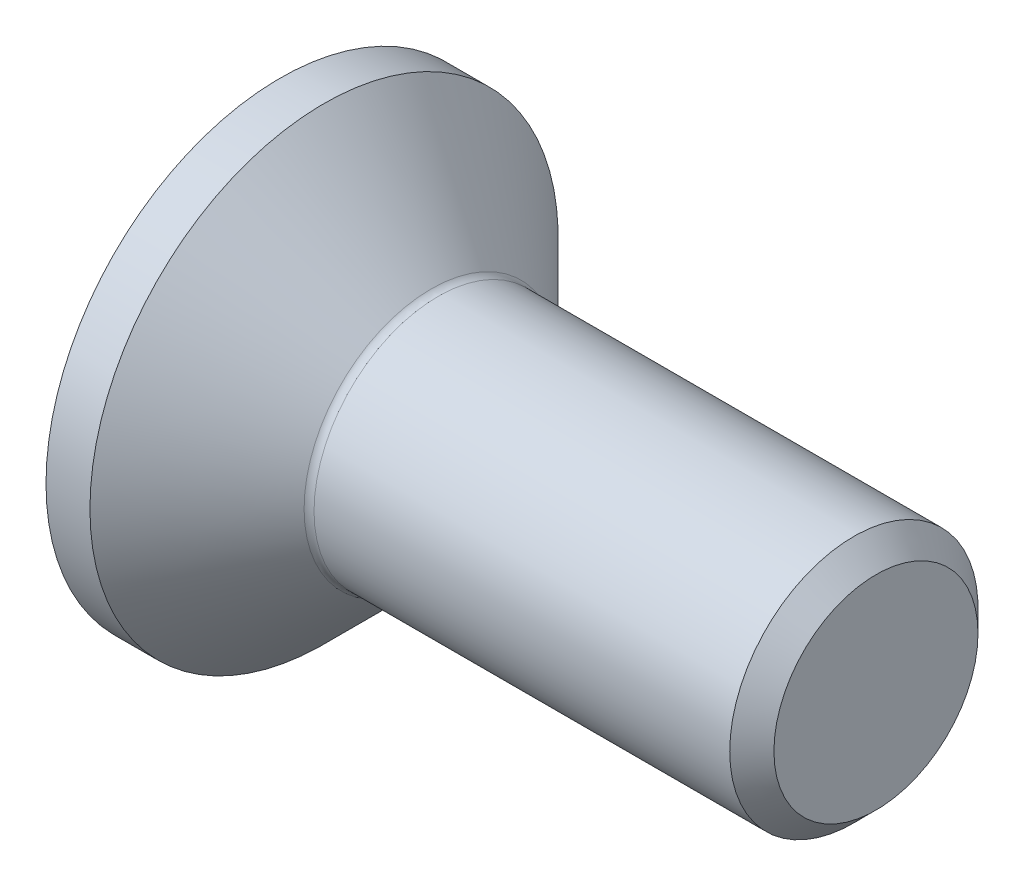
SolidWorks part; units mm, degrees
ref_plane "Plane1" through (0, 0, 0) normal (0, 0, 1) x (1, 0, 0)
ref_plane "Plane2" through (0, 0, 0) normal (0, 1, 0) x (1, 0, 0)
ref_plane "Plane3" through (0, 0, 0) normal (1, 0, 0) x (0, 0, -1)
sketch "BodySke" plane through (0, 0, 0) normal (0, 0, 1) x (1, 0, 0)
  line L0 (0, 0) -> (0, 4.715)
  line L1 (0.885, 4.715) -> (3.1, 2.5)
  line L2 (0, 4.715) -> (0.885, 4.715)
  line L3 (3.1, 2.5) -> (11.555, 2.5)
  line L4 (12, 2.055) -> (12, 0)
  line L5 (12, 0) -> (0, 0)
  line L6 (0, 0) -> (127, 0) construction
  line L7 (0.885, -4.715) -> (3.1, -2.5) construction
  line L8 (12, 2.055) -> (11.555, 2.5)
  line L9 (0, -4.715) -> (0.885, -4.715) construction
  line L10 (12, -2.055) -> (11.555, -2.5) construction
  line L11 (3.9, 8.85) -> (3.9, -13.375) construction
  line L12 (0, 19.05) -> (0, -3.175) construction
  dimension "D1" = 0.885
  dimension "Diameter" = 5
  dimension "Head_ht" = 3.1
  dimension "Length" = 12
  dimension "Body_ch_ang" = 45
  dimension "Head_dia" = 9.43
  dimension "Minor_dia" = 4.11
  dimension "Head_ang" = 90
  dimension "Advance" = 0.8
  dimension "Thread_nom" = 12
revolve "BaseBody" add sketch "BodySke"
cosmetic thread "ThreadCosmetic" [suppressed]
fillet "Fillet1" radius 0.2 1 edges at (3.1, 0, 2.5)
sketch "Sketch2" plane through (0, 0, 0) normal (0, 0, 1) x (1, 0, 0)
  line L0 (0, 1.5) -> (1.9, 1.5)
  line L1 (1.9, 1.5) -> (2.766, 0)
  line L2 (0, 0) -> (127, 0) construction
  line L3 (2.766, 0) -> (0, 0)
  line L4 (0, 0) -> (0, 1.5)
  line L5 (0, -1.5) -> (1.9, -1.5) construction
  line L6 (0, 0) -> (47.625, 0) construction
  line L8 (0, 4.715) -> (0, -4.715) construction
  dimension "D2" = 60
  dimension "PreBroach_depth" = 1.9
  dimension "PreBroach_dia" = 3
revolve "PreBroach" cut sketch "Sketch2" angle 360 about L6
sketch "Sketch3" plane through (0, 0, 0) normal (-1, 0, 0) x (0, 0, 1)
  line L0 (-1.5, -0.866) -> (-1.5, 0.866)
  line L1 (-1.5, 0.866) -> (0, 1.7321)
  line L2 (0, 1.7321) -> (1.5, 0.866)
  line L3 (1.5, 0.866) -> (1.5, -0.866)
  line L4 (1.5, -0.866) -> (0, -1.7321)
  line L5 (0, -1.7321) -> (-1.5, -0.866)
  dimension "D1" = 1.5
  dimension "D2" = 1.5
  dimension "D3" = 3
  dimension "Hex_size" = 3
extrude "Hex" cut sketch "Sketch3" against normal blind 1.9
sketch "ThdSchSke" [suppressed] plane through (0, 0, 0) normal (0, 0, 1) x (1, 0, 0)
  line L0 (5.5, -2.055) -> (5.1884, -2.5)
  line L1 (5.5, -2.055) -> (5.8116, -2.5)
  line L2 (5.8116, -2.5) -> (5.8116, -3.125)
  line L3 (-3.175, 0) -> (5.1513, 0) construction
  line L4 (0, 4.715) -> (0, -4.715) construction
  line L5 (5.8116, -3.125) -> (5.1884, -3.125)
  line L6 (5.1884, -3.125) -> (5.1884, -2.5)
  dimension "Thread_minor" = 4.11
  dimension "Diameter" = 5
  dimension "Start" = 5.5
  dimension "SideAngle" = 55
  dimension "VeeAngle" = 70
  dimension "Overcut" = 6.25
revolve "ThreadSchematic" [suppressed] cut sketch "ThdSchSke" angle 360 about L3
pattern_linear "ThdSchPat" [suppressed]
equation "\"Thread_minor@ThreadCosmetic\"  =  \"Minor_dia@BodySke\""
equation "\"D1@Sketch3\" = \"Hex_size@Sketch3\" / 2"
equation "\"D2@Sketch3\" = \"D1@Sketch3\""
equation "\"D3@Sketch3\" = \"Hex_size@Sketch3\""
equation "\"Thread_length@ThreadCosmetic\" = ((sgn( (\"Length@BodySke\" - \"Advance@BodySke\" * 3.0 - \"Head_ht@BodySke\" ) - \"Thread_nom@BodySke\" )-1)*( (\"Length@BodySke\" - \"Advance@BodySke\" * 3.0 - \"Head_ht@BodySke\" ) - \"Thread_nom@BodySke\" ))/-2+ \"Thread_nom@BodySke\""
equation "\"Thread_minor@ThdSchSke\" = \"Minor_dia@BodySke\""
equation "\"Diameter@ThdSchSke\" = \"Diameter@BodySke\""
equation "\"Overcut@ThdSchSke\" = \"Diameter@BodySke\" * 1.25"
equation "\"Start@ThdSchSke\" = 0.000001 + \"Length@BodySke\" - \"Thread_length@ThreadCosmetic\"  '---Countersunk---"
equation "\"Num_threads@ThdSchPat\" = int( \"Thread_length@ThreadCosmetic\" / \"Advance@BodySke\" + 0.999 )  + 1"
equation "\"Advance@ThdSchPat\" = \"Thread_length@ThreadCosmetic\" /  (\"Num_threads@ThdSchPat\" - 1) 'relax it"
equation "\"Num_threads@ThdSchPat\" = \"Num_threads@ThdSchPat\" - sgn( \"Num_threads@ThdSchPat\" - 1) '---chamfered tips only---"
